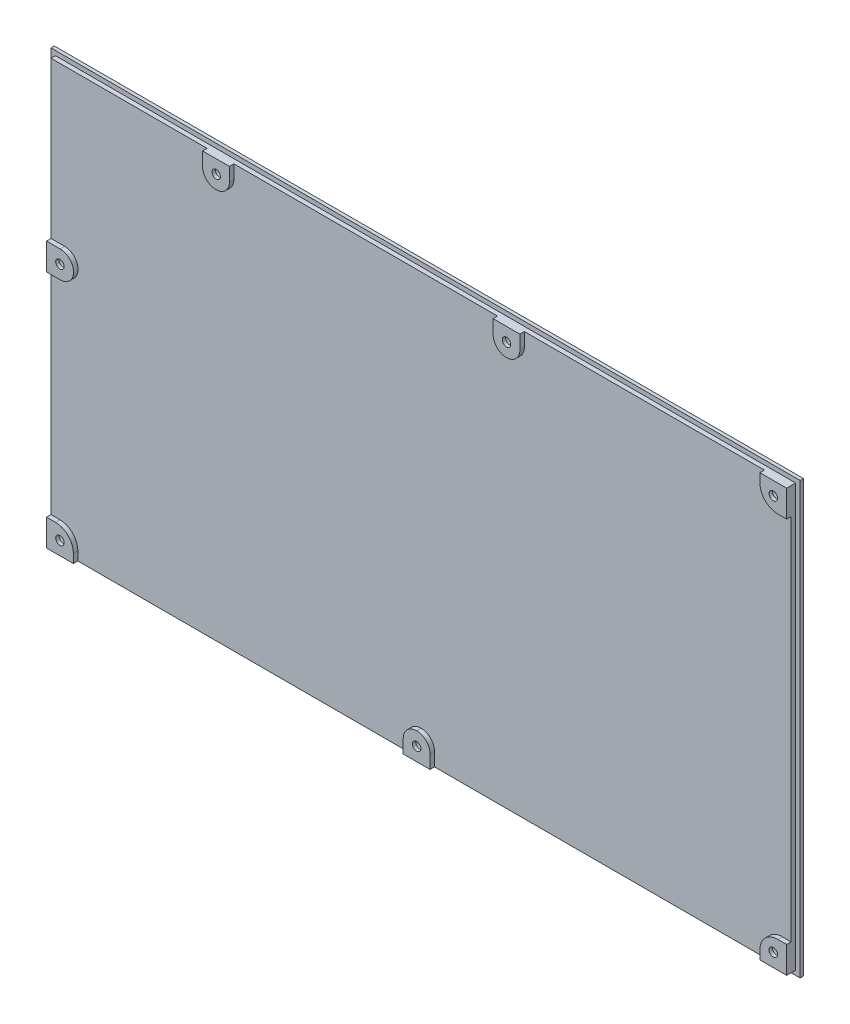
SolidWorks part; units mm, degrees
ref_plane "Front Plane" through (0, 0, 0) normal (0, 0, 1) x (1, 0, 0)
ref_plane "Top Plane" through (0, 0, 0) normal (0, 1, 0) x (1, 0, 0)
ref_plane "Right Plane" through (0, 0, 0) normal (1, 0, 0) x (0, 0, -1)
sketch "Sketch1" plane through (0, 0, 0) normal (0, 0, 1) x (1, 0, 0)
  line L1 (-167.75, -96.5) -> (167.75, -96.5)
  line L2 (-167.75, -96.5) -> (-167.75, 96.5)
  line L3 (-167.75, 96.5) -> (167.75, 96.5)
  line L4 (167.75, -96.5) -> (167.75, 96.5)
  line L5 (-167.75, -96.5) -> (167.75, 96.5) construction
  line L6 (-167.75, 96.5) -> (167.75, -96.5) construction
  point P0 (0, 0)
  dimension "D1" = 193
  dimension "D2" = 335.5
extrude "Boss-Extrude1" add sketch "Sketch1" along normal blind 1.5
sketch "Sketch2" plane through (0, 0, 1.5) normal (0, 0, 1) x (1, 0, 0)
  line L0 (167.75, 96.5) -> (-167.75, 96.5) construction
  line L1 (-165.75, -94.5) -> (165.75, -94.5)
  line L2 (-165.75, -94.5) -> (-165.75, 94.5)
  line L3 (-165.75, 94.5) -> (165.75, 94.5)
  line L4 (165.75, -94.5) -> (165.75, 94.5)
  line L5 (-165.75, -94.5) -> (165.75, 94.5) construction
  line L6 (-165.75, 94.5) -> (165.75, -94.5) construction
  line L7 (-167.75, 96.5) -> (-167.75, -96.5) construction
  line L8 (-153.75, -82.5) -> (-153.75, 82.5) construction
  line L9 (-165.75, 94.5) -> (-153.75, 94.5)
  line L10 (-165.75, 94.5) -> (-165.75, 82.5)
  line L13 (165.75, 94.5) -> (153.75, 94.5)
  line L14 (165.75, 94.5) -> (165.75, 82.5)
  line L15 (165.75, 82.5) -> (161.75, 82.5)
  line L16 (153.75, 94.5) -> (153.75, 90.5)
  line L17 (165.75, -94.5) -> (153.75, -94.5)
  line L18 (165.75, -94.5) -> (165.75, -82.5)
  line L19 (165.75, -82.5) -> (161.75, -82.5)
  line L20 (153.75, -94.5) -> (153.75, -90.5)
  line L21 (-165.75, -94.5) -> (-153.75, -94.5)
  line L22 (-165.75, -94.5) -> (-165.75, -82.5)
  line L23 (-165.75, -82.5) -> (-161.75, -82.5)
  line L24 (-153.75, -94.5) -> (-153.75, -90.5)
  line L25 (-153.75, 82.5) -> (153.75, 82.5) construction
  line L26 (153.75, 82.5) -> (153.75, -82.5) construction
  line L27 (153.75, -82.5) -> (-153.75, -82.5) construction
  line L32 (6, 94.5) -> (-6, 94.5)
  line L36 (0.1, -82.5) -> (-0.1, -82.5)
  line L37 (6, -88.4) -> (6, -94.5)
  line L38 (6, -94.5) -> (-6, -94.5)
  line L39 (-6, -88.4) -> (-6, -94.5)
  line L40 (6, -82.5) -> (-6, -94.5) construction
  line L41 (6, -94.5) -> (-6, -82.5) construction
  arc A0 (161.75, 82.5) -> (153.75, 90.5) centre (161.75, 90.5) cw
  arc A1 (161.75, -82.5) -> (153.75, -90.5) centre (161.75, -90.5) ccw
  arc A2 (-161.75, -82.5) -> (-153.75, -90.5) centre (-161.75, -90.5) cw
  arc A4 (-0.1, -82.5) -> (-6, -88.4) centre (-0.1, -88.4) ccw
  arc A5 (0.1, -82.5) -> (6, -88.4) centre (0.1, -88.4) cw
  point P0 (0, 0)
  point P29 (0, -88.5)
  dimension "D9" = 8
  dimension "D10" = 5.9
  dimension "D1" = 2
  dimension "D2" = 2
  dimension "D3" = 12
  dimension "D4" = 12
  dimension "D5" = 12
  dimension "D6" = 12
  dimension "D8" = 12
extrude "Boss-Extrude2" add sketch "Sketch2" along normal blind 2
sketch "Sketch4" plane through (0, 0, 1.5) normal (0, 0, 1) x (1, 0, 0)
  line L0 (-165.75, -82.5) -> (-165.75, -94.5)
  line L1 (-165.75, -94.5) -> (-153.75, -94.5)
  line L2 (-165.75, -82.5) -> (-161.75, -82.5) construction
  line L3 (-153.75, -94.5) -> (-153.75, -90.5) construction
  line L4 (-6, -88.4) -> (-6, -94.5) construction
  line L5 (6, -88.4) -> (6, -94.5) construction
  line L6 (0.1, -82.5) -> (-0.1, -82.5) construction
  line L7 (153.75, -94.5) -> (153.75, -90.5) construction
  line L8 (165.75, -82.5) -> (161.75, -82.5) construction
  line L9 (165.75, 82.5) -> (161.75, 82.5) construction
  line L10 (153.75, 94.5) -> (153.75, 90.5) construction
  line L11 (-165.75, -82.5) -> (-165.75, 94.5) construction
  line L16 (-165.75, -82.5) -> (-161.75, -82.5)
  line L17 (-153.75, -94.5) -> (-153.75, -90.5)
  line L18 (-6, -88.4) -> (-6, -94.5)
  line L19 (6, -88.4) -> (6, -94.5)
  line L20 (0.1, -82.5) -> (-0.1, -82.5)
  line L21 (153.75, -94.5) -> (153.75, -90.5)
  line L22 (165.75, -82.5) -> (161.75, -82.5)
  line L23 (165.75, 82.5) -> (161.75, 82.5)
  line L24 (153.75, 94.5) -> (153.75, 90.5)
  line L25 (46.25, 88.4) -> (46.25, 94.5)
  line L26 (34.25, 88.4) -> (34.25, 94.5)
  line L28 (-83.85, 88.4) -> (-83.85, 94.5)
  line L29 (-95.85, 88.4) -> (-95.85, 94.5)
  line L30 (-89.75, 82.5) -> (-89.95, 82.5)
  line L31 (-95.85, 94.5) -> (-83.85, 94.5)
  line L32 (-165.75, 94.5) -> (153.75, 94.5) construction
  line L33 (34.25, 94.5) -> (46.25, 94.5)
  line L34 (153.75, 94.5) -> (165.75, 94.5)
  line L35 (165.75, 94.5) -> (165.75, 82.5)
  line L36 (153.75, -94.5) -> (165.75, -94.5)
  line L37 (165.75, -94.5) -> (165.75, -82.5)
  line L38 (-6, -94.5) -> (6, -94.5)
  line L39 (-165.75, -82.5) -> (-165.75, 94.5) construction
  line L40 (-150.5818, -94.5) -> (-150.5818, -88.4) construction
  line L42 (-159.65, 24.6) -> (-165.75, 24.6)
  line L44 (-153.75, -94.5) -> (-6, -94.5) construction
  line L45 (159.75, -94.5) -> (159.75, -88.5) construction
  line L46 (-159.65, 12.6) -> (-165.75, 12.6)
  line L47 (-165.75, 24.6) -> (-165.75, 12.6)
  line L48 (-165.75, 94.5) -> (153.75, 94.5) construction
  arc A0 (-153.75, -90.5) -> (-161.75, -82.5) centre (-161.75, -90.5) ccw construction
  arc A1 (-0.1, -82.5) -> (-6, -88.4) centre (-0.1, -88.4) ccw construction
  arc A2 (6, -88.4) -> (0.1, -82.5) centre (0.1, -88.4) ccw construction
  arc A3 (161.75, -82.5) -> (153.75, -90.5) centre (161.75, -90.5) ccw construction
  arc A4 (153.75, 90.5) -> (161.75, 82.5) centre (161.75, 90.5) ccw construction
  arc A5 (46.25, 88.4) -> (34.25, 88.4) centre (40.25, 88.4) cw
  arc A8 (-153.75, -90.5) -> (-161.75, -82.5) centre (-161.75, -90.5) ccw
  arc A9 (-0.1, -82.5) -> (-6, -88.4) centre (-0.1, -88.4) ccw
  arc A10 (6, -88.4) -> (0.1, -82.5) centre (0.1, -88.4) ccw
  arc A11 (161.75, -82.5) -> (153.75, -90.5) centre (161.75, -90.5) ccw
  arc A12 (153.75, 90.5) -> (161.75, 82.5) centre (161.75, 90.5) ccw
  arc A15 (-89.75, 82.5) -> (-83.85, 88.4) centre (-89.75, 88.4) ccw
  arc A16 (-159.65, 12.6) -> (-159.65, 24.6) centre (-159.65, 18.6) ccw
  arc A17 (-95.85, 88.4) -> (-89.95, 82.5) centre (-89.95, 88.4) ccw
  line M5 (-165.75, 94.5) -> (153.75, 94.5)
  line M6 (153.75, 94.5) -> (153.75, 90.5)
  arc M7 (153.75, 90.5) -> (161.75, 82.5) centre (161.75, 90.5) ccw
  line M8 (161.75, 82.5) -> (165.75, 82.5)
  line M10 (165.75, -82.5) -> (161.75, -82.5)
  arc M11 (161.75, -82.5) -> (153.75, -90.5) centre (161.75, -90.5) ccw
  line M12 (153.75, -90.5) -> (153.75, -94.5)
  line M14 (6, -94.5) -> (6, -88.4)
  arc M15 (6, -88.4) -> (0.1, -82.5) centre (0.1, -88.4) ccw
  line M16 (0.1, -82.5) -> (-0.1, -82.5)
  arc M17 (-0.1, -82.5) -> (-6, -88.4) centre (-0.1, -88.4) ccw
  line M18 (-6, -88.4) -> (-6, -94.5)
  line M20 (-153.75, -94.5) -> (-153.75, -90.5)
  arc M21 (-153.75, -90.5) -> (-161.75, -82.5) centre (-161.75, -90.5) ccw
  line M22 (-161.75, -82.5) -> (-165.75, -82.5)
  line M23 (-165.75, -82.5) -> (-165.75, 94.5)
  line M27 (-165.75, 94.5) -> (153.75, 94.5)
  dimension "D1" = 6.1
  dimension "D2" = 12
  dimension "D6" = 5.9
  dimension "D10" = 206
  dimension "D3" = 6
  dimension "D4" = 6.1
  dimension "D5" = 107
  dimension "D7" = 6.1
  dimension "D8" = 12
  dimension "D9" = 76
  dimension "D11" = 6.1
  dimension "D12" = 12
extrude "Boss-Extrude3" add sketch "Sketch4" along normal blind 4 contours L0 L1 M20 M21 M22 | L38 M18 M14 M15 M16 M17 | L36 L37 M10 M11 M12 | L35 L34 M6 M7 M8 | L46 A16 L42 M23 | L29 A17 L30 A15 L28 M27 | A5 L25 L26 M5
sketch "Sketch5" plane through (0, 0, 0) normal (0, 0, -1) x (-1, 0, 0)
  line L0 (-167.75, 88.5) -> (167.75, 88.5) construction
  line L1 (-167.75, -96.5) -> (-167.75, 96.5) construction
  line L2 (167.75, 96.5) -> (167.75, -96.5) construction
  line L3 (-167.75, -88.5) -> (167.75, -88.5) construction
  line L4 (-167.75, 96.5) -> (167.75, 96.5) construction
  line L5 (167.75, -96.5) -> (-167.75, -96.5) construction
  line L6 (159.75, 88.5) -> (159.75, 18.6) construction
  line L7 (165.75, 24.6) -> (165.75, 94.5) construction
  line L8 (153.65, 18.6) -> (159.75, 18.6) construction
  circle A0 centre (-159.75, 88.5) radius 4
  circle A1 centre (0, 88.5) radius 4 construction
  circle A2 centre (0, -88.5) radius 4
  circle A3 centre (159.75, 88.5) radius 4 construction
  circle A4 centre (159.75, -88.5) radius 4
  circle A5 centre (-159.75, -88.5) radius 4
  circle A6 centre (89.75, 88.5) radius 4
  circle A7 centre (-40.25, 88.4) radius 4
  circle A8 centre (159.75, 18.6) radius 4
  arc A9 (159.65, 24.6) -> (159.65, 12.6) centre (159.65, 18.6) ccw construction
  dimension "D3" = 8
  dimension "D4" = 8
  dimension "D5" = 8
  dimension "D8" = 8
  dimension "D1" = 8
  dimension "D2" = 8
  dimension "D6" = 8
  dimension "D7" = 8
  dimension "D9" = 76
extrude "Cut-Extrude1" cut sketch "Sketch5" against normal blind 4
sketch "Sketch6" plane through (0, 0, 0) normal (0, 0, -1) x (-1, 0, 0)
  circle A0 centre (-159.75, -88.5) radius 1.9
  circle A1 centre (0, -88.5) radius 1.9
  circle A2 centre (159.75, -88.5) radius 1.9
  circle A3 centre (159.75, 88.5) radius 1.9 construction
  circle A4 centre (0, 88.5) radius 1.9 construction
  circle A5 centre (-159.75, 88.5) radius 1.9
  circle A6 centre (89.75, 88.5) radius 1.9
  circle A7 centre (159.75, 18.6) radius 1.9
  circle A8 centre (-40.25, 88.4) radius 1.9
  dimension "D1" = 3.8
extrude "Cut-Extrude2" cut sketch "Sketch6" against normal blind 14
